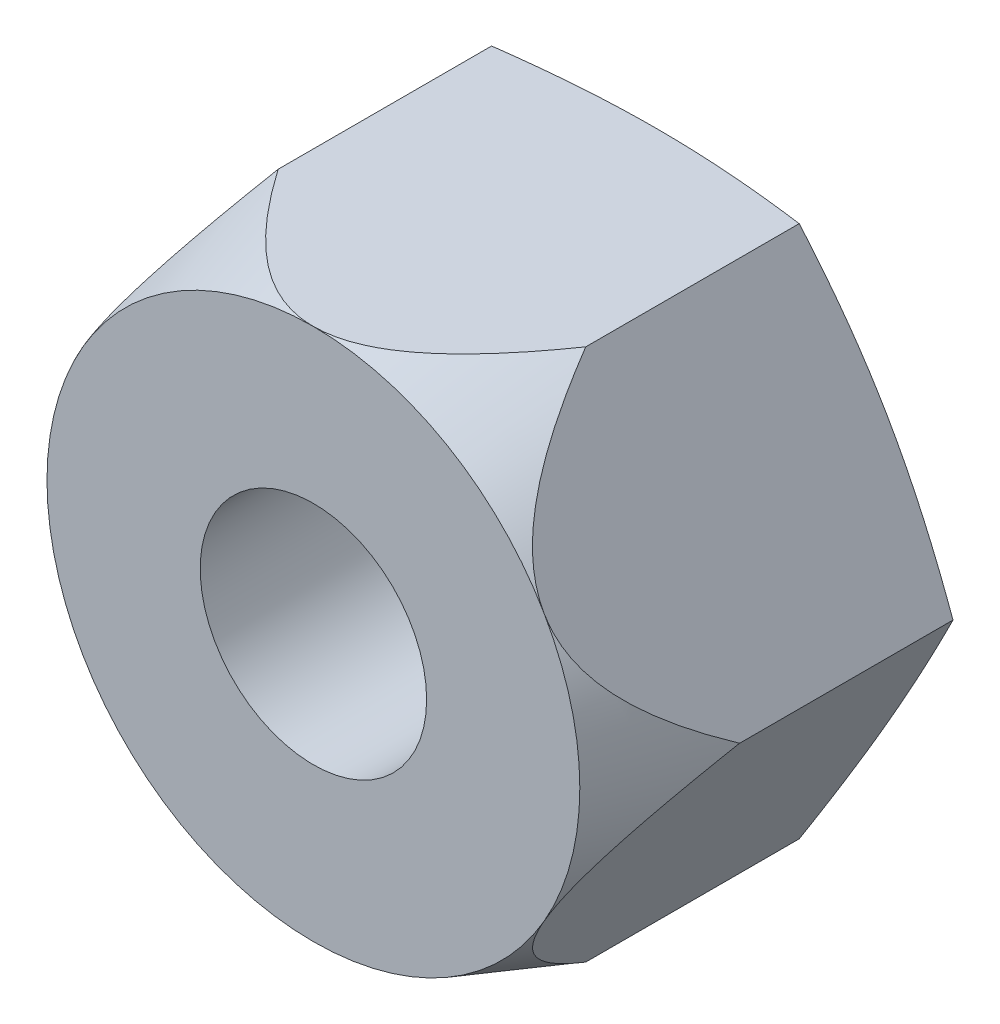
SolidWorks part; units mm, degrees
ref_plane "Front" through (0, 0, 0) normal (0, 0, 1) x (1, 0, 0)
ref_plane "Top" through (0, 0, 0) normal (0, 1, 0) x (1, 0, 0)
ref_plane "Right" through (0, 0, 0) normal (1, 0, 0) x (0, 0, -1)
sketch "Sketch1" plane through (0, 0, 0) normal (0, 0, 1) x (1, 0, 0)
  line L1 (2.3094, -4) -> (4.6188, 0)
  line L2 (4.6188, 0) -> (2.3094, 4)
  line L3 (2.3094, 4) -> (-2.3094, 4)
  line L4 (-2.3094, 4) -> (-4.6188, 0)
  line L5 (-4.6188, 0) -> (-2.3094, -4)
  line L6 (-2.3094, -4) -> (2.3094, -4)
  circle A0 centre (0, 0) radius 4 construction
  dimension "s" = 8
extrude "BaseNut" add sketch "Sketch1" against normal blind 5.3
sketch "Sketch2" plane through (0.4812, 0, -5.1) normal (0, -1, 0) x (0, 0, -1)
  line L0 (-0.1158, 4.1376) -> (0.2, 4.1376)
  line L2 (0.2, 4.1376) -> (0.2, 2.9588)
  line L3 (-5.1, 1.8282) -> (-5.1, 4.1376) construction
  line L4 (0.2, 2.9588) -> (-0.1158, 4.1376)
  line L5 (-5.1, 4.1376) -> (-3.32, 4.1376)
  line L6 (-5.1, 4.1376) -> (-5.1, 3.5188)
  line L7 (0.2, 1.8282) -> (0.2, 4.1376) construction
  line L8 (-5.1, 3.5188) -> (-3.32, 4.1376)
  line L9 (-0.6371, -0.4812) -> (-5.5811, -0.4812) construction
  line L10 (0.2, 4.1376) -> (-5.1, 4.1376) construction
  dimension "e" = 8
  dimension "D" = 6.88
  dimension "D4" = 15
  dimension "m1" = 3.52
revolve "Double-Chamfer" cut sketch "Sketch2" angle 360 about L9
sketch "Sketch3" plane through (0, 0, 0) normal (0, 0, 1) x (1, 0, 0)
  circle A0 centre (0, 0) radius 1.7
  dimension "D1" = 3.4
extrude "Hole" cut sketch "Sketch3" against normal through all
cosmetic thread "ThreadCosmetic1" [suppressed] parameters "D2"=5
chamfer "EndChamfer" distance 0.4857 angle 45 1 edges at (1.7, 0, -5.3)
sketch "Sketch4" plane through (0, 0, 0) normal (0, 1, 0) x (1, 0, 0)
  line L0 (0, 6.8088) -> (0, -0.7438) construction
  line L1 (0.9, 5.2143) -> (1.7, 5.2143)
  line L2 (1.7, 5.2143) -> (2.3928, 4.8143)
  line L3 (2.3928, 4.8143) -> (1.7, 4.4143)
  line L4 (1.7, 4.4143) -> (0.9, 4.4143)
  line L5 (0.9, 4.4143) -> (0.9, 5.2143)
  line L6 (-1.7, 4.8143) -> (1.7, 4.8143) construction
  dimension "D1" = 3.4
  dimension "D2" = 0.8
revolve "Cut-Revolve10" [suppressed] cut sketch "Sketch4" angle 360 about L0
pattern_linear "LPattern10" [suppressed] count 5 spacing 0.96 along (0, 0, 1)
equation "\"e@Sketch2\" = \"s@Sketch1\""
equation "\"D1@Sketch4\" = \"D1@Sketch3\""
equation "\"D2@Sketch4\" = (  \"D2@ThreadCosmetic1\" - \"D1@Sketch3\" )  / 2"
equation "\"D3@LPattern10\" = \"D2@Sketch4\" * 1.2"
equation "\"D1@LPattern10\" =  ( \"h@BaseNut\" - \"D1@EndChamfer\"  ) / \"D3@LPattern10\""
equation "\"D1@EndChamfer\" = \"D1@Sketch3\" / 7"
